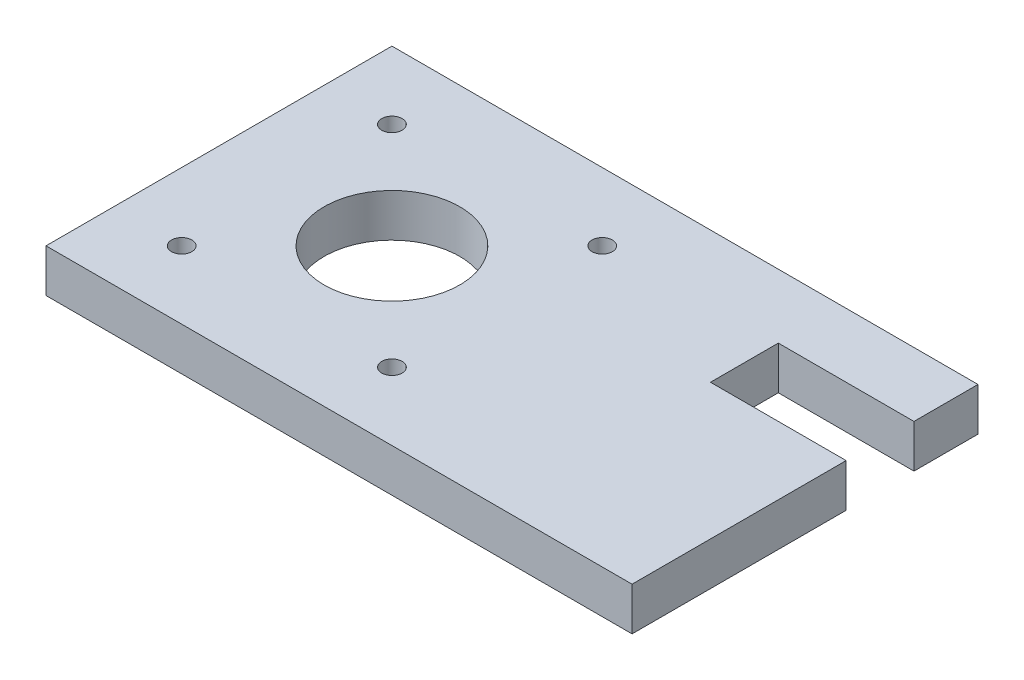
SolidWorks part; units mm, degrees
ref_plane "Front Plane" through (0, 0, 0) normal (0, 0, 1) x (1, 0, 0)
ref_plane "Top Plane" through (0, 0, 0) normal (0, 1, 0) x (1, 0, 0)
ref_plane "Right Plane" through (0, 0, 0) normal (1, 0, 0) x (0, 0, -1)
sketch "Sketch1" plane through (0, 0, 0) normal (0, 1, 0) x (1, 0, 0)
  line L0 (-25.5, 25.5) -> (-25.5, -25.5)
  line L5 (-15.5, -15.5) -> (15.5, -15.5) construction
  line L6 (-15.5, -15.5) -> (-15.5, 15.5) construction
  line L7 (-15.5, 15.5) -> (15.5, 15.5) construction
  line L8 (15.5, -15.5) -> (15.5, 15.5) construction
  line L9 (-15.5, -15.5) -> (15.5, 15.5) construction
  line L10 (-15.5, 15.5) -> (15.5, -15.5) construction
  line L11 (-25.5, -25.5) -> (50.9, -25.5)
  line L14 (60.9, 25.5) -> (-25.5, 25.5)
  line L15 (0, 6) -> (97.9193, 6) construction
  line L16 (0, -6) -> (97.9193, -6) construction
  line L17 (38.2, -25.5) -> (38.2, 25.5) construction
  line L19 (25.5, -25.5) -> (25.5, 25.5) construction
  line L22 (50.9, -25.5) -> (50.9, 25.5) construction
  line L23 (60.9, 25.5) -> (60.9, 16.0618)
  line L24 (60.9, -25.5) -> (50.9, -25.5)
  line L25 (20.2838, 11.0618) -> (60.9, 11.0618) construction
  line L26 (20.2838, 1.0618) -> (60.9, 1.0618) construction
  line L27 (20.2838, 1.0618) -> (20.2838, 21.0618) construction
  line L28 (20.2838, 21.0618) -> (60.9, 21.0618) construction
  line L29 (60.9, 1.0618) -> (60.9, 6.0618) construction
  line L30 (60.9, 6.0618) -> (60.9, -25.5)
  line L31 (60.9, 6.0618) -> (40.9, 6.0618)
  line L33 (60.9, 16.0618) -> (40.9, 16.0618)
  line L34 (40.9, 6.0618) -> (40.9, 16.0618)
  line L35 (60.9, 16.0618) -> (60.9, 21.0618) construction
  circle A0 centre (0, 0) radius 6 construction
  circle A1 centre (-15.5, 15.5) radius 1.5
  circle A2 centre (15.5, 15.5) radius 1.5
  circle A3 centre (15.5, -15.5) radius 1.5
  circle A4 centre (-15.5, -15.5) radius 1.5
  circle A5 centre (0, 0) radius 10
  point P0 (0, 0)
  point P37 (40.9, 11.0618)
  dimension "D2" = 12
  dimension "D8" = 3
  dimension "D9" = 20
  dimension "D13" = 20
  dimension "D1" = 31
  dimension "D3" = 20
  dimension "D4" = 10
  dimension "D5" = 10
  dimension "D6" = 25.4
  dimension "D7" = 10
  dimension "D10" = 10
  dimension "D11" = 10
  dimension "D12" = 10
extrude "Boss-Extrude1" add sketch "Sketch1" along normal blind 6.35
